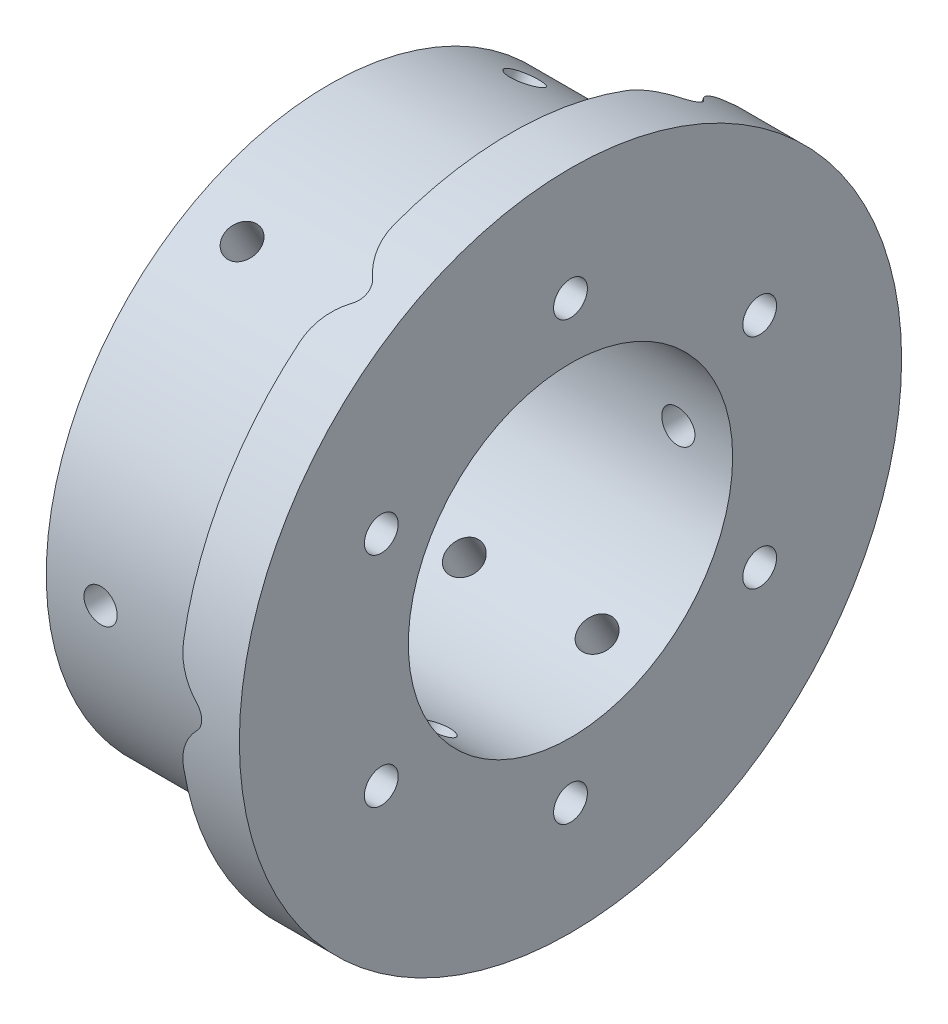
SolidWorks part; units mm, degrees
ref_plane "Front Plane" through (0, 0, 0) normal (0, 0, 1) x (1, 0, 0)
ref_plane "Top Plane" through (0, 0, 0) normal (0, 1, 0) x (1, 0, 0)
ref_plane "Right Plane" through (0, 0, 0) normal (1, 0, 0) x (0, 0, -1)
sketch "Sketch1" plane through (0, 0, 0) normal (1, 0, 0) x (0, 0, -1)
  circle A0 centre (0, 0) radius 13.435
  circle A1 centre (0, 0) radius 23.435
  circle A2 centre (0, 0) radius 18.1 construction
  circle A3 centre (0, 18.1) radius 1.4
  circle A4 centre (15.6751, 9.05) radius 1.4
  circle A5 centre (15.6751, -9.05) radius 1.4
  circle A6 centre (0, -18.1) radius 1.4
  circle A7 centre (-15.6751, -9.05) radius 1.4
  circle A8 centre (-15.6751, 9.05) radius 1.4
  point P9 (-26.1475, 14.4334)
  point P10 (0, 0)
  point P20 (0, 0)
  dimension "D1" = 10
  dimension "D2" = 26.87
  dimension "D3" = 36.2
  dimension "D4" = 2.8
  dimension "D5" = 6
extrude "Boss-Extrude1" add sketch "Sketch1" along normal mid plane 20
sketch "Sketch4" plane through (10, 0, 0) normal (1, 0, 0) x (0, 0, -1)
  circle A0 centre (0, 0) radius 23.435 construction
  circle A1 centre (0, 0) radius 23.435
  circle A2 centre (0, 0) radius 27.435
  dimension "D1" = 4
extrude "Boss-Extrude2" add sketch "Sketch4" against normal blind 5
sketch "Sketch3" plane through (0, 0, 0) normal (0, 0, 1) x (1, 0, 0)
  circle A0 centre (5.5, 0) radius 1.375
  point P2 (0, 0)
  dimension "D1" = 5.5
  dimension "D2" = 2.75
extrude "Cut-Extrude1" cut sketch "Sketch3" against normal through all
pattern_circular "CirPattern1" count 6 over 360 about axis through (10, 0, 0) along (-1, 0, 0) of "Cut-Extrude1"
pattern_linear "LPattern1" count 2 spacing 11 along (-1, 0, 0) of "CirPattern1", "Cut-Extrude1"
fillet "Fillet1" radius 5 12 edges at (5, -21.3588, 13.8105) (5, -22.6397, 11.592) (5, 1.2809, 25.4025) (5, -1.2809, 25.4025) (5, -21.3588, -13.8105) (5, -22.6397, -11.592) (5, 22.6397, 11.592) (5, 21.3588, 13.8105) (5, 21.3588, -13.8105) (5, 22.6397, -11.592) (5, -1.2809, -25.4025) (5, 1.2809, -25.4025)
